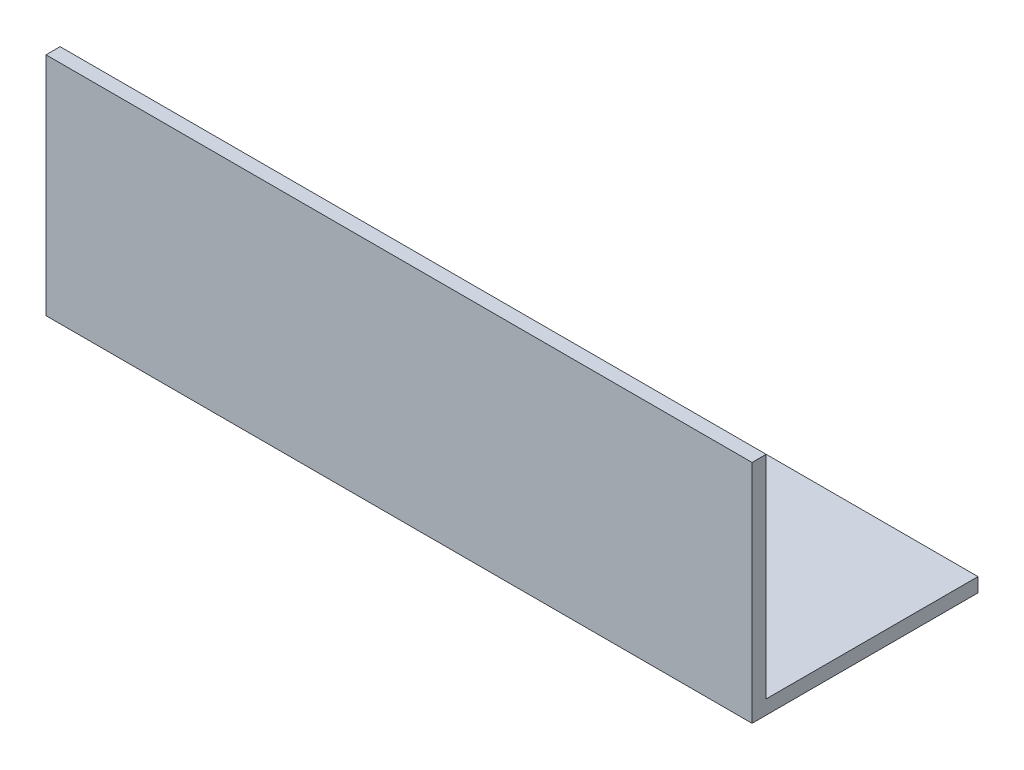
SolidWorks part; units mm, degrees
ref_plane "Спереди" through (0, 0, 0) normal (0, 0, 1) x (1, 0, 0)
ref_plane "Сверху" through (0, 0, 0) normal (0, 1, 0) x (1, 0, 0)
ref_plane "Справа" through (0, 0, 0) normal (1, 0, 0) x (0, 0, -1)
sketch "Эскиз1" plane through (0, 0, 0) normal (1, 0, 0) x (0, 0, -1)
  line L0 (0, 45) -> (0, 0)
  line L1 (0, 0) -> (45, 0)
extrude "Вытянуть-Тонкостенный1" add sketch "Эскиз1" along normal blind 150 thin
